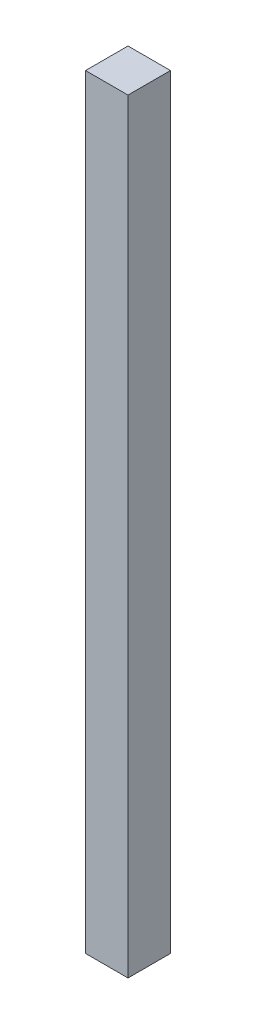
SolidWorks part; units mm, degrees
ref_plane "Front Plane" through (0, 0, 0) normal (0, 0, 1) x (1, 0, 0)
ref_plane "Top Plane" through (0, 0, 0) normal (0, 1, 0) x (1, 0, 0)
ref_plane "Right Plane" through (0, 0, 0) normal (1, 0, 0) x (0, 0, -1)
sketch "Sketch1" plane through (0, 0, 0) normal (0, 1, 0) x (1, 0, 0)
  line L1 (0, 0) -> (25.4, 0)
  line L2 (0, 0) -> (0, 25.4)
  line L3 (0, 25.4) -> (25.4, 25.4)
  line L4 (25.4, 0) -> (25.4, 25.4)
  dimension "D1" = 25.4
  dimension "D2" = 25.4
extrude "Boss-Extrude1" add sketch "Sketch1" along normal blind 457.2
